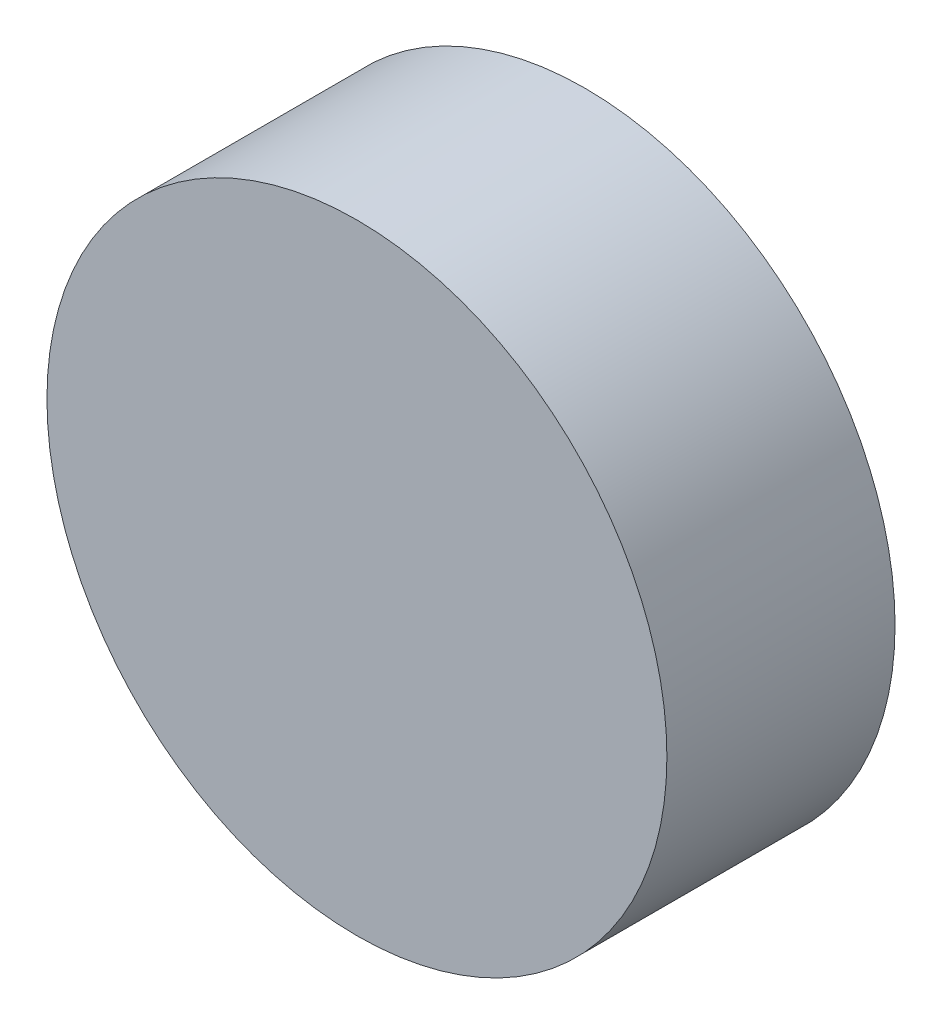
SolidWorks part; units mm, degrees
ref_plane "Front Plane" through (0, 0, 0) normal (0, 0, 1) x (1, 0, 0)
ref_plane "Top Plane" through (0, 0, 0) normal (0, 1, 0) x (1, 0, 0)
ref_plane "Right Plane" through (0, 0, 0) normal (1, 0, 0) x (0, 0, -1)
sketch "Sketch1" plane through (0, 0, 0) normal (0, 0, 1) x (1, 0, 0)
  circle A0 centre (-128.2934, -1.5034) radius 47.625
  dimension "D1" = 95.25
extrude "Boss-Extrude1" add sketch "Sketch1" along normal blind 35.052
